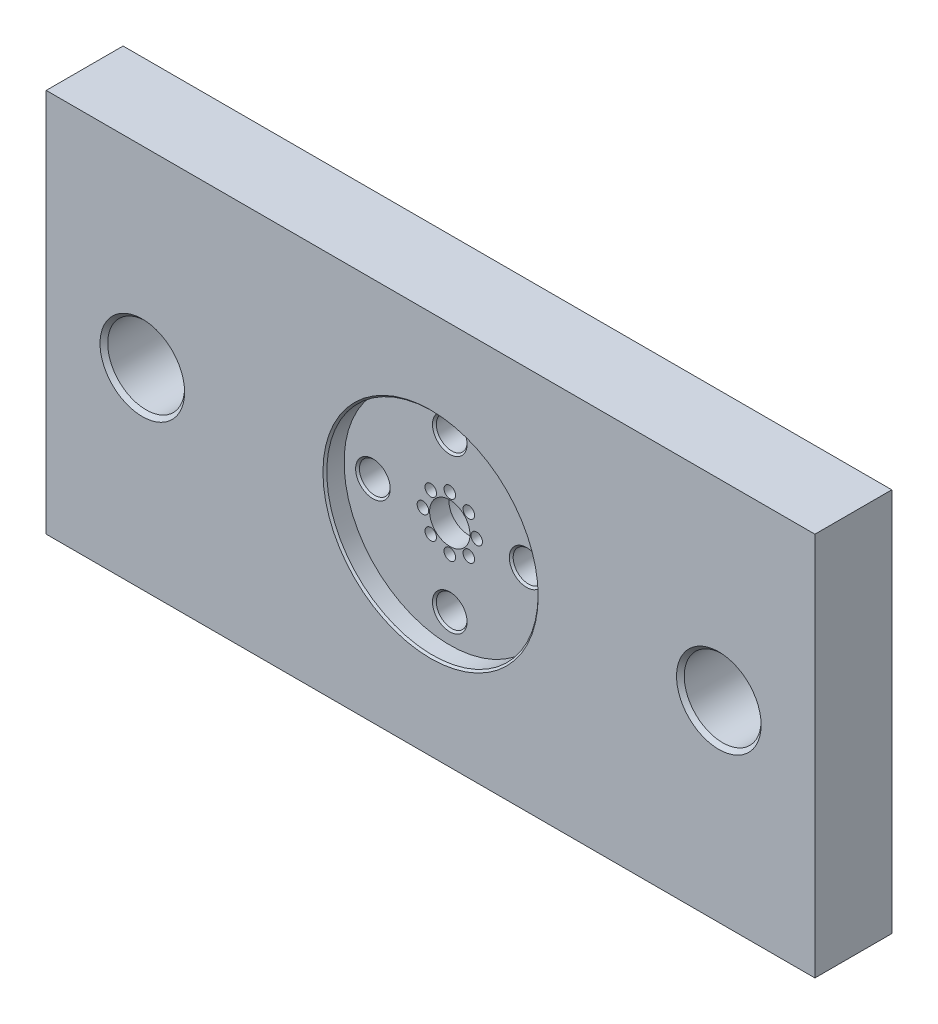
SolidWorks part; units mm, degrees
ref_plane "Front Plane" through (0, 0, 0) normal (0, 0, 1) x (1, 0, 0)
ref_plane "Top Plane" through (0, 0, 0) normal (0, 1, 0) x (1, 0, 0)
ref_plane "Right Plane" through (0, 0, 0) normal (1, 0, 0) x (0, 0, -1)
sketch "Sketch1" plane through (0, 0, 0) normal (0, 0, 1) x (1, 0, 0)
  line L0 (0, 0) -> (0, 47614.3041) construction
  line L1 (0, 0) -> (-47614.3041, 0) construction
  line L3 (100, -50) -> (-100, -50)
  line L4 (100, -50) -> (100, 50)
  line L5 (100, 50) -> (-100, 50)
  line L6 (-100, -50) -> (-100, 50)
  line L7 (100, -50) -> (-100, 50) construction
  line L8 (100, 50) -> (-100, -50) construction
  point P5 (0, 0)
  dimension "D1" = 100
  dimension "D2" = 200
extrude "Boss-Extrude1" add sketch "Sketch1" against normal blind 20
sketch "Sketch2" plane through (0, 0, 0) normal (0, 0, 1) x (1, 0, 0)
  circle A0 centre (0, 0) radius 27.5
  dimension "D1" = 55
extrude "Cut-Extrude1" cut sketch "Sketch2" against normal blind 5
sketch "Sketch3" plane through (0, 0, -5) normal (0, 0, 1) x (1, 0, 0)
  line L0 (0, 0) -> (0, 50000) construction
  line L1 (0, 0) -> (-50000, 0) construction
  circle A0 centre (-20, 0) radius 4
  circle A1 centre (0, 20) radius 4
  circle A2 centre (20, 0) radius 4
  circle A3 centre (0, -20) radius 4
  circle A4 centre (0, 0) radius 5.25
  point P15 (0, 0)
  dimension "D1" = 8
  dimension "D4" = 10.5
  dimension "D2" = 20
  dimension "D3" = 4
extrude "Cut-Extrude2" cut sketch "Sketch3" against normal through all
sketch "Sketch4" plane through (0, 0, -20) normal (0, 0, -1) x (-1, 0, 0)
  line L0 (0, 0) -> (0, 50000) construction
  line L1 (0, 0) -> (-50000, 0) construction
  circle A0 centre (0, 20) radius 6.5
  circle A1 centre (20, 0) radius 6.5
  circle A2 centre (0, -20) radius 6.5
  circle A3 centre (-20, 0) radius 6.5
  point P12 (0, 0)
  dimension "D1" = 13
  dimension "D2" = 4
extrude "Cut-Extrude3" cut sketch "Sketch4" against normal blind 8
chamfer "Chamfer1" distance 0.5 angle 45 13 edges at (4, -20, -5) (-16, 0, -5) (4, 20, -5) (24, 0, -5) (16, 0, -12) (13.5, 0, -20) (-4, -20, -12) (-6.5, -20, -20) (-24, 0, -12) (-26.5, 0, -20) (-4, 20, -12) (-6.5, 20, -20) (27.5, 0, 0)
sketch "Sketch5" plane through (0, 0, 0) normal (0, 0, 1) x (1, 0, 0)
  line L0 (0, 0) -> (0, 50000) construction
  line L1 (0, 0) -> (-50000, 0) construction
  circle A0 centre (75, 0) radius 10
  circle A1 centre (-75, 0) radius 10
  point P9 (0, 0)
  point P10 (0, 0)
  dimension "D1" = 20
  dimension "D6" = 20
  dimension "D2" = 75
  dimension "D5" = 75
extrude "Cut-Extrude4" cut sketch "Sketch5" against normal through all
chamfer "Chamfer2" distance 1 angle 45 4 edges at (85, 0, 0) (-65, 0, 0) (-65, 0, -20) (85, 0, -20)
sketch "Sketch7" plane through (0, 0, -20) normal (0, 0, -1) x (-1, 0, 0)
  circle A0 centre (0, 0) radius 11
  dimension "D1" = 22
extrude "Cut-Extrude5" cut sketch "Sketch7" against normal blind 10
chamfer "Chamfer3" distance 0.5 angle 45 1 edges at (-11, 0, -10)
sketch "Sketch8" plane through (0, 0, -5) normal (0, 0, 1) x (1, 0, 0)
  line L0 (0, 0) -> (0, 50000) construction
  line L1 (0, 0) -> (-50000, 0) construction
  circle A0 centre (0, 0) radius 7 construction
  circle A2 centre (0, 7) radius 1.5
  circle A3 centre (4.9497, 4.9497) radius 1.5
  circle A4 centre (7, 0) radius 1.5
  circle A5 centre (4.9497, -4.9497) radius 1.5
  circle A6 centre (0, -7) radius 1.5
  circle A7 centre (-4.9497, -4.9497) radius 1.5
  circle A8 centre (-7, 0) radius 1.5
  circle A9 centre (-4.9497, 4.9497) radius 1.5
  point P10 (0, 0)
  point P11 (0, 0)
  point P25 (0, 0)
  dimension "D1" = 14
  dimension "D2" = 3
  dimension "D3" = 8
extrude "Cut-Extrude6" cut sketch "Sketch8" against normal through all
